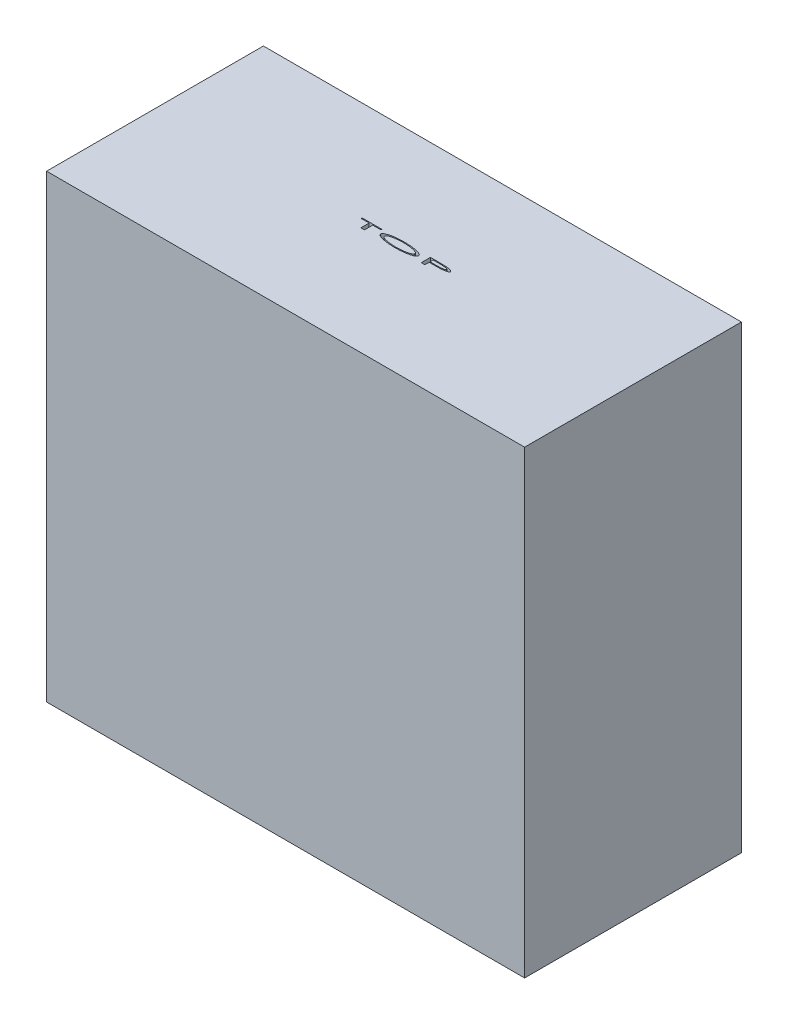
SolidWorks part; units mm, degrees
ref_plane "Front Plane" through (0, 0, 0) normal (0, 0, 1) x (1, 0, 0)
ref_plane "Top Plane" through (0, 0, 0) normal (0, 1, 0) x (1, 0, 0)
ref_plane "Right Plane" through (0, 0, 0) normal (1, 0, 0) x (0, 0, -1)
sketch "Sketch1" plane through (0, 0, 0) normal (0, 1, 0) x (1, 0, 0)
  line L1 (91.5, 41.5) -> (-91.5, 41.5)
  line L2 (91.5, 41.5) -> (91.5, -41.5)
  line L3 (91.5, -41.5) -> (-91.5, -41.5)
  line L4 (-91.5, 41.5) -> (-91.5, -41.5)
  line L5 (91.5, 41.5) -> (-91.5, -41.5) construction
  line L6 (91.5, -41.5) -> (-91.5, 41.5) construction
  point P0 (0, 0)
  dimension "D1" = 83
  dimension "D2" = 183
extrude "Boss-Extrude1" add sketch "Sketch1" along normal blind 176
sketch "Sketch5" plane through (0, 176, 0) normal (0, 1, 0) x (1, 0, 0)
  text T0 "TOP" font "Century Gothic" height 3.5
extrude "Cut-Extrude1" cut sketch "Sketch5" against normal blind 5
